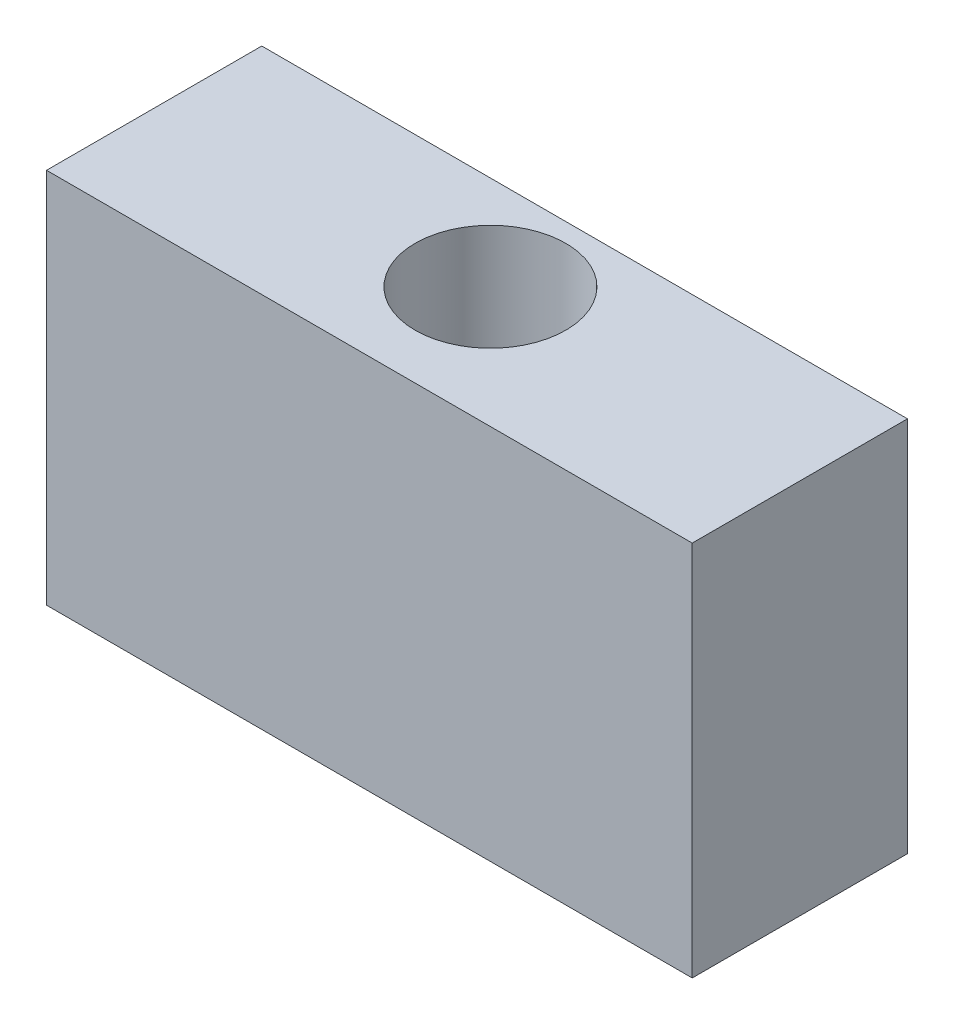
SolidWorks part; units mm, degrees
material "Polyethylene Cross-Linked"
ref_plane "Front Plane" through (0, 0, 0) normal (0, 0, 1) x (1, 0, 0)
ref_plane "Top Plane" through (0, 0, 0) normal (0, 1, 0) x (1, 0, 0)
ref_plane "Right Plane" through (0, 0, 0) normal (1, 0, 0) x (0, 0, -1)
sketch "Sketch1" plane through (0, 0, 0) normal (0, 1, 0) x (1, 0, 0)
  line L1 (0, 0) -> (38.1, 0)
  line L2 (0, 0) -> (0, 12.7)
  line L3 (0, 12.7) -> (38.1, 12.7)
  line L4 (38.1, 0) -> (38.1, 12.7)
  circle A0 centre (19.05, 7.1437) radius 4.445
extrude "Boss-Extrude1" add sketch "Sketch1" along normal blind 22.225
